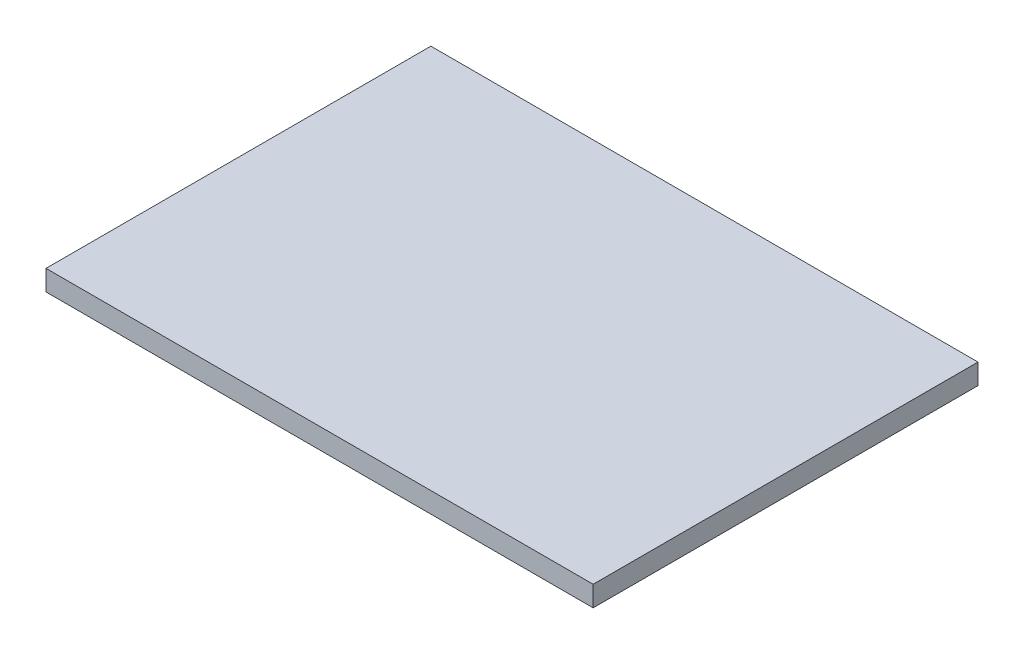
SolidWorks part; units mm, degrees
ref_plane "Front Plane" through (0, 0, 0) normal (0, 0, 1) x (1, 0, 0)
ref_plane "Top Plane" through (0, 0, 0) normal (0, 1, 0) x (1, 0, 0)
ref_plane "Right Plane" through (0, 0, 0) normal (1, 0, 0) x (0, 0, -1)
sketch "Sketch1" plane through (0, 0, 0) normal (0, 1, 0) x (1, 0, 0)
  line L1 (-187.325, -131.7625) -> (187.325, -131.7625)
  line L2 (-187.325, -131.7625) -> (-187.325, 131.7625)
  line L3 (-187.325, 131.7625) -> (187.325, 131.7625)
  line L4 (187.325, -131.7625) -> (187.325, 131.7625)
  line L5 (-187.325, -131.7625) -> (187.325, 131.7625) construction
  line L6 (-187.325, 131.7625) -> (187.325, -131.7625) construction
  point P0 (0, 0)
  dimension "D1" = 374.65
  dimension "D2" = 263.525
extrude "Boss-Extrude1" add sketch "Sketch1" along normal blind 14
